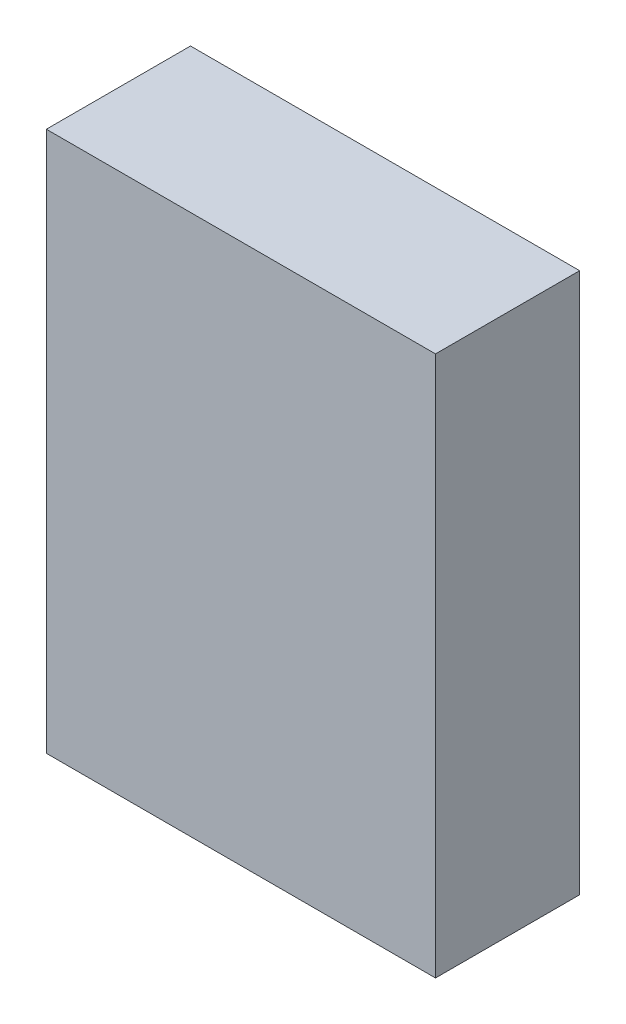
SolidWorks part; units mm, degrees
ref_plane "Front Plane" through (0, 0, 0) normal (0, 0, 1) x (1, 0, 0)
ref_plane "Top Plane" through (0, 0, 0) normal (0, 1, 0) x (1, 0, 0)
ref_plane "Right Plane" through (0, 0, 0) normal (1, 0, 0) x (0, 0, -1)
sketch "Sketch1" plane through (0, 0, 0) normal (0, 0, 1) x (1, 0, 0)
  line L1 (0, 0) -> (10.8, 0)
  line L2 (0, 0) -> (0, 15)
  line L3 (0, 15) -> (10.8, 15)
  line L4 (10.8, 0) -> (10.8, 15)
  dimension "D1" = 10.8
  dimension "D2" = 15
extrude "Boss-Extrude1" add sketch "Sketch1" along normal blind 4
